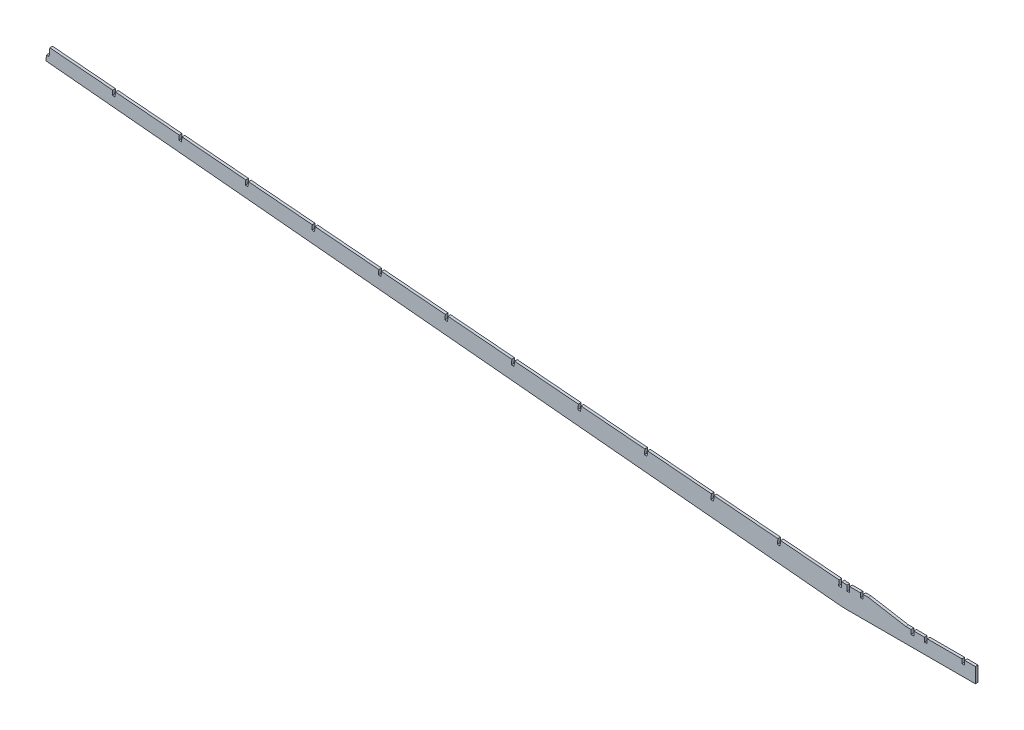
SolidWorks part; units mm, degrees
material "Plywood"
ref_plane "Front Plane" through (0, 0, 0) normal (0, 0, 1) x (1, 0, 0)
ref_plane "Top Plane" through (0, 0, 0) normal (0, 1, 0) x (1, 0, 0)
ref_plane "Right Plane" through (0, 0, 0) normal (1, 0, 0) x (0, 0, -1)
sketch "Sketch1" plane through (0, 0, 0) normal (0, 0, 1) x (1, 0, 0)
  line L0 (-951.0618, 63.2916) -> (-11.5367, -24.9026)
  line L8 (-8.3728, -25.1683) -> (-6.7788, -6.1851) construction
  line L9 (-6.7788, -6.1851) -> (-9.9426, -5.9194)
  line L10 (-9.9426, -5.9194) -> (-11.5367, -24.9026) construction
  line L11 (-11.5367, -24.9026) -> (-8.3728, -25.1683)
  line L12 (3.175, -25.5459) -> (3.175, -6.4959) construction
  line L13 (3.175, -6.4959) -> (0, -6.4959)
  line L14 (0, -6.4959) -> (0, -25.5459) construction
  line L15 (0, -25.5459) -> (3.175, -25.5459)
  line L17 (-943.9754, 109.7383) -> (-947.3666, 69.3536)
  line L19 (-8.3728, -25.1683) -> (0, -25.5459)
  line L20 (3.175, -25.5459) -> (152.4, -25.5459)
  line L21 (25.4, -0.1459) -> (69.85, -7.7659)
  line L22 (25.4, -0.1459) -> (-2.8123, -0.1459)
  line L23 (-2.8123, -0.1459) -> (-946.5481, 79.1019)
  line L24 (0, -6.4959) -> (0, -0.1459)
  line L25 (3.175, -6.4959) -> (3.175, -0.1459)
  line L26 (-6.7788, -6.1851) -> (-6.2474, 0.1426)
  line L27 (-9.9426, -5.9194) -> (-9.4113, 0.4083)
  line L28 (-9.9426, -5.9194) -> (-946.998, 73.7432)
  line L29 (69.85, -7.7659) -> (152.4, -7.7659)
  line L30 (152.4, -7.7659) -> (152.4, -25.5459)
  line L31 (76.2, -7.7659) -> (76.2, -25.5459)
  line L32 (79.375, -7.7659) -> (79.375, -25.5459)
  line L33 (76.2, -12.8459) -> (79.375, -12.8459)
  line L34 (15.875, -0.1459) -> (15.875, -5.2259)
  line L35 (15.875, -5.2259) -> (19.05, -5.2259)
  line L36 (19.05, -5.2259) -> (19.05, -0.1459)
  line L37 (92.075, -7.7659) -> (92.075, -12.8459)
  line L38 (92.075, -12.8459) -> (95.25, -12.8459)
  line L39 (95.25, -12.8459) -> (95.25, -7.7659)
  line L40 (136.525, -7.7659) -> (136.525, -12.8459)
  line L41 (136.525, -12.8459) -> (139.7, -12.8459)
  line L42 (139.7, -12.8459) -> (139.7, -7.7659)
  line L44 (-951.0618, 63.2916) -> (-950.5305, 69.6193)
  line L45 (-950.5305, 69.6193) -> (-947.3666, 69.3536)
  dimension "D1" = 25.4
  dimension "D2" = 6.35
extrude "Boss-Extrude1" add sketch "Sketch1" along normal blind 3.175
sketch "Sketch2" plane through (0, 0, 3.175) normal (0, 0, 1) x (1, 0, 0)
  line L1 (-73.9963, 64.5177) -> (-80.9723, -18.558)
  line L3 (-77.1601, 64.7834) -> (-84.1362, -18.2923)
  line L5 (-153.17, 68.7234) -> (-159.8855, -11.2491)
  line L7 (-232.3428, 72.9404) -> (-238.7996, -3.951)
  line L9 (-311.5203, 77.1018) -> (-317.7101, 3.3887)
  line L11 (-390.6978, 81.2631) -> (-396.6209, 10.7264)
  line L13 (-469.8812, 85.3537) -> (-475.5272, 18.1169)
  line L15 (-549.0652, 89.4374) -> (-554.4332, 25.5108)
  line L17 (-628.256, 93.4393) -> (-633.334, 32.9679)
  line L19 (-707.4489, 97.4177) -> (-712.2332, 40.4425)
  line L21 (-786.6506, 101.2897) -> (-791.1254, 48.0007)
  line L23 (-865.8569, 105.1088) -> (-870.014, 55.603)
  line L25 (-235.5067, 73.2061) -> (-241.9634, -3.6853)
  line L27 (-314.6841, 77.3675) -> (-320.874, 3.6544)
  line L29 (-393.8616, 81.5287) -> (-399.7848, 10.992)
  line L31 (-473.045, 85.6194) -> (-478.6911, 18.3826)
  line L33 (-552.229, 89.7031) -> (-557.5971, 25.7765)
  line L35 (-631.4199, 93.705) -> (-636.4978, 33.2336)
  line L37 (-710.6127, 97.6833) -> (-715.3971, 40.7082)
  line L39 (-789.8145, 101.5554) -> (-794.2893, 48.2664)
  line L41 (-9.9426, -5.9194) -> (-946.998, 73.7432)
  line L43 (-9.4113, 0.4083) -> (-946.5481, 79.1019)
  line L45 (-156.3339, 68.9891) -> (-163.0494, -10.9834)
  line L47 (-869.0207, 105.3745) -> (-873.1778, 55.8686)
extrude "Cut-Extrude1" cut sketch "Sketch2" against normal through all
move or copy body "Body-Move/Copy1" [suppressed] bodies to move or copy 102 parameters "D1"=0, "D2"=0, "D3"=0
